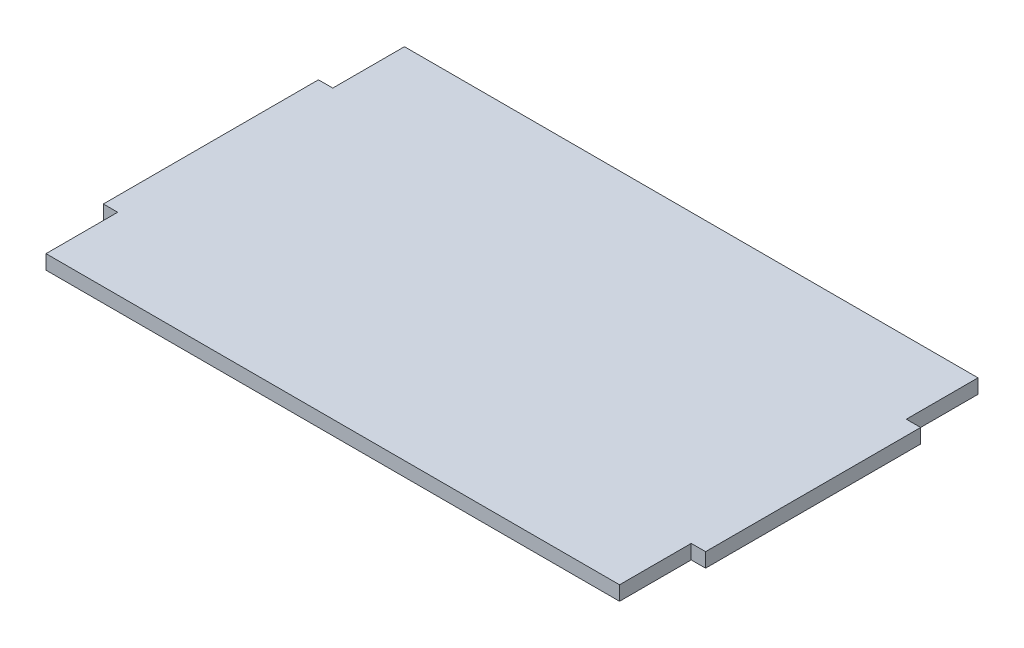
SolidWorks part; units mm, degrees
ref_plane "Front Plane" through (0, 0, 0) normal (0, 0, 1) x (1, 0, 0)
ref_plane "Top Plane" through (0, 0, 0) normal (0, 1, 0) x (1, 0, 0)
ref_plane "Right Plane" through (0, 0, 0) normal (1, 0, 0) x (0, 0, -1)
sketch "Sketch2" plane through (0, 0, 0) normal (0, 1, 0) x (1, 0, 0)
  line L0 (0, -50) -> (160, -50) construction
  line L1 (0, 0) -> (160, 0)
  line L2 (0, 0) -> (0, -20)
  line L3 (0, -100) -> (160, -100)
  line L4 (160, 0) -> (160, -20)
  line L5 (0, -20) -> (-4, -20)
  line L6 (80, 0) -> (80, -66.6608) construction
  line L7 (-4, -80) -> (-4, -20)
  line L8 (0, -80) -> (-4, -80)
  line L9 (160, -80) -> (164, -80)
  line L10 (160, -20) -> (164, -20)
  line L11 (164, -80) -> (164, -20)
  line L12 (0, -80) -> (0, -100)
  line L13 (160, -80) -> (160, -100)
  dimension "D1" = 100
  dimension "D2" = 168
  dimension "D3" = 4
  dimension "D4" = 168
extrude "Boss-Extrude1" add sketch "Sketch2" along normal blind 4
